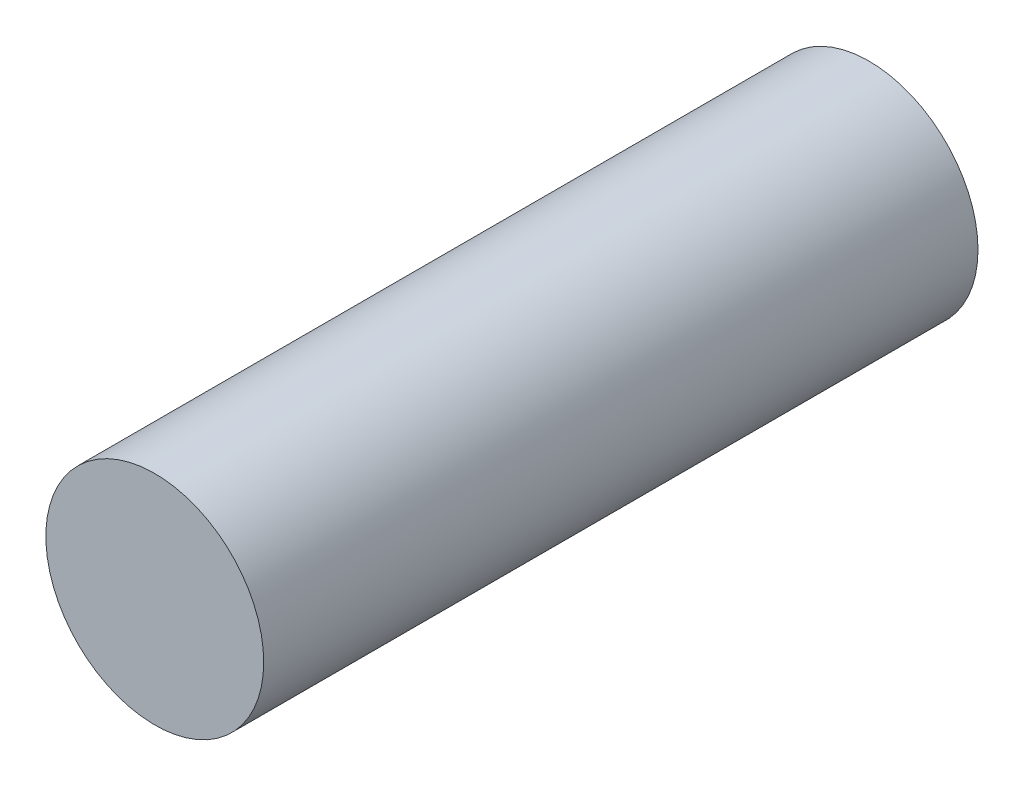
SolidWorks part; units mm, degrees
ref_plane "Front Plane" through (0, 0, 0) normal (0, 0, 1) x (1, 0, 0)
ref_plane "Top Plane" through (0, 0, 0) normal (0, 1, 0) x (1, 0, 0)
ref_plane "Right Plane" through (0, 0, 0) normal (1, 0, 0) x (0, 0, -1)
sketch "Sketch1" plane through (0, 0, 0) normal (0, 0, 1) x (1, 0, 0)
  circle A0 centre (8.5, 4) radius 3.05
extrude "Boss-Extrude1" add sketch "Sketch1" along normal blind 3 and the other way blind 17 contours A0
